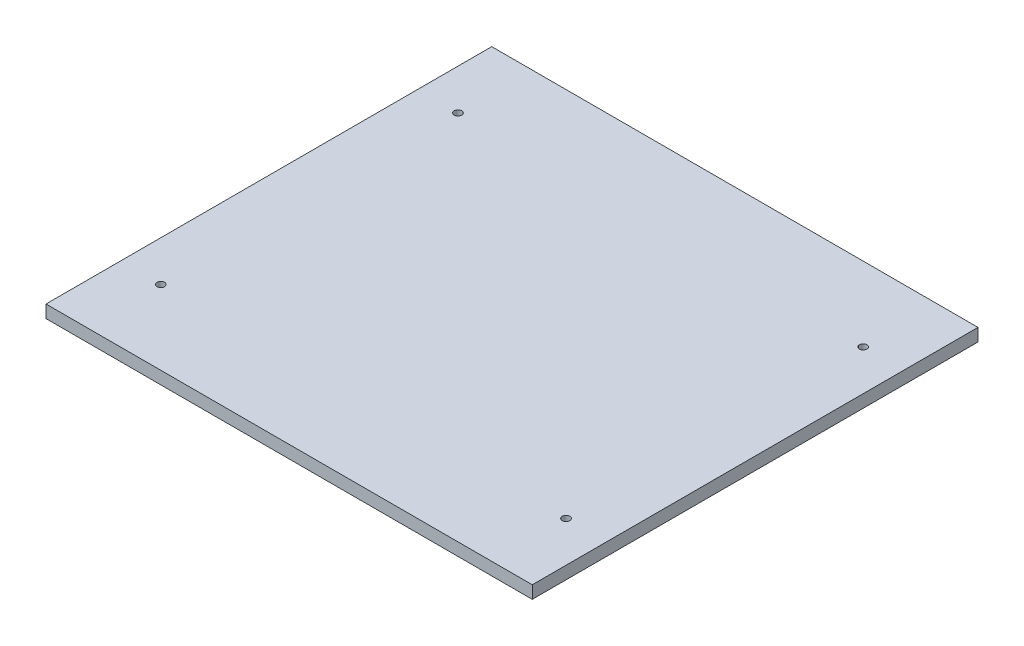
SolidWorks part; units mm, degrees
material "Pine"
ref_plane "Front Plane" through (0, 0, 0) normal (0, 0, 1) x (1, 0, 0)
ref_plane "Top Plane" through (0, 0, 0) normal (0, 1, 0) x (1, 0, 0)
ref_plane "Right Plane" through (0, 0, 0) normal (1, 0, 0) x (0, 0, -1)
sketch "Sketch1" plane through (0, 0, 0) normal (0, 1, 0) x (1, 0, 0)
  line L1 (-228.6, -209.55) -> (228.6, -209.55)
  line L2 (-228.6, -209.55) -> (-228.6, 209.55)
  line L3 (-228.6, 209.55) -> (228.6, 209.55)
  line L4 (228.6, -209.55) -> (228.6, 209.55)
  line L5 (-228.6, -209.55) -> (228.6, 209.55) construction
  line L6 (-228.6, 209.55) -> (228.6, -209.55) construction
  point P0 (0, 0)
  dimension "D1" = 419.1
  dimension "D2" = 457.2
extrude "Boss-Extrude1" add sketch "Sketch1" along normal blind 11.9062
sketch "Sketch2" plane through (0, 11.9062, 0) normal (0, 1, 0) x (1, 0, 0)
  line L0 (-228.6, -209.55) -> (228.6, -209.55) construction
  point P0 (-190.5, -139.7)
  point P1 (190.5, -139.7)
  point P2 (-190.5, 139.7)
  point P3 (190.5, 139.7)
  dimension "D1" = 381
  dimension "D2" = 190.5
  dimension "D3" = 279.4
  dimension "D4" = 69.85
hole_wizard "9/32 (0.28125) Diameter Hole1" positions "Sketch3" profile "Sketch4" hole size "9/32" standard "ANSI Inch" end condition through all
sketch "Sketch3" plane through (0, 11.9062, 0) normal (0, 1, 0) x (1, 0, 0)
  point P0 (-190.5, 139.7)
  point P3 (190.5, 139.7)
  point P6 (190.5, -139.7)
  point P9 (-190.5, -139.7)
sketch "Sketch4" plane through (-190.5, 11.9062, -139.7) normal (1, 0, 0) x (0, 0, 1)
  line L0 (0, 0) -> (0, 11.9062)
  line L1 (0, 11.9062) -> (3.5719, 11.9062)
  line L2 (3.5719, 11.9062) -> (3.5719, 0)
  line L5 (3.5719, 0) -> (0, 0)
  line L11 (0, -6.35) -> (0, 107.95) construction
  dimension "Thru Hole Dia." = 7.1437
  dimension "Thru Hole Depth" = 11.9062
